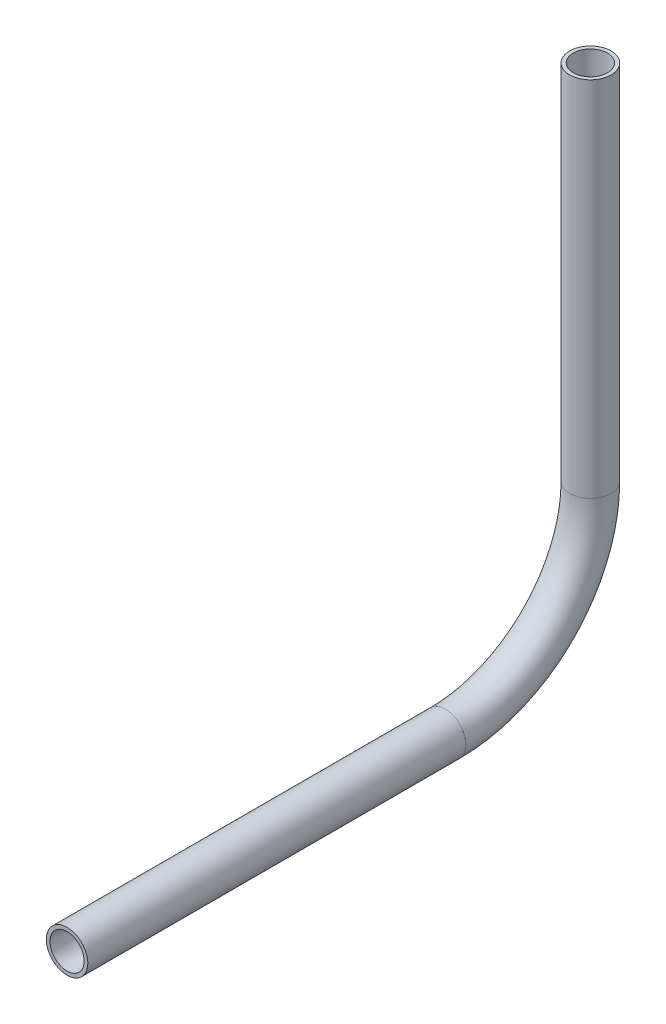
SolidWorks part; units mm, degrees
ref_plane "Front Plane" through (0, 0, 0) normal (0, 0, 1) x (1, 0, 0)
ref_plane "Top Plane" through (0, 0, 0) normal (0, 1, 0) x (1, 0, 0)
ref_plane "Right Plane" through (0, 0, 0) normal (1, 0, 0) x (0, 0, -1)
sketch "Sketch1" plane through (0, 0, 0) normal (1, 0, 0) x (0, 0, -1)
  line L0 (-132.6345, 251.5055) -> (-74.7675, 251.5055)
  line L1 (-52.5425, 273.7305) -> (-52.5425, 329.2006)
  arc A0 (-74.7675, 251.5055) -> (-52.5425, 273.7305) centre (-74.7675, 273.7305) ccw
  point P2 (-67.0857, 260.1703)
  point P6 (-74.7675, 251.5055)
  dimension "D1" = 22.225
other "Pipe 0.5 SCH 40(1)"
ref_plane "Plane1" through (0, 251.5055, 132.6345) normal (0, 0, -1) x (0, 1, 0)
sketch "Sketch11" plane through (0, 251.5055, 132.6345) normal (0, 0, -1) x (0, 1, 0)
  circle A0 centre (0, 0) radius 3.175
  circle A1 centre (0, 0) radius 2.6162
  point P5 (0, 0)
  dimension "In_dia" = 6.35
  dimension "Out_dia" = 5.2324
